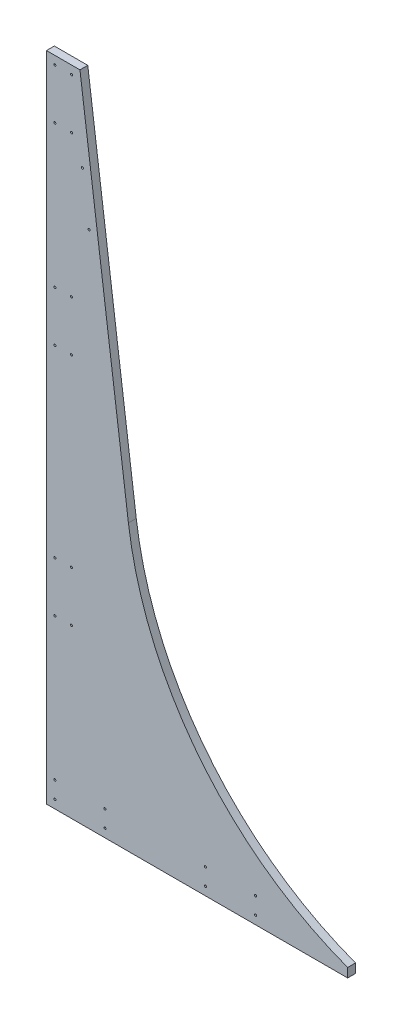
SolidWorks part; units mm, degrees
material "Pine"
ref_plane "Front Plane" through (0, 0, 0) normal (0, 0, 1) x (1, 0, 0)
ref_plane "Top Plane" through (0, 0, 0) normal (0, 1, 0) x (1, 0, 0)
ref_plane "Right Plane" through (0, 0, 0) normal (1, 0, 0) x (0, 0, -1)
sketch "Sketch1" plane through (0, 0, 0) normal (0, 0, 1) x (1, 0, 0)
  line L0 (0, 0) -> (500, 0)
  line L1 (0, 0) -> (0, 990.6)
  line L3 (0, 990.6) -> (50.8, 990.6)
  line L4 (50.8, 990.6) -> (124.3674, 431.8)
  line L7 (457.201, 13.862) -> (457.201, 0)
  arc A9 (124.3674, 431.8) -> (500, 0) centre (638.1166, 499.4364) ccw
  dimension "D18" = 50.8
  dimension "D1" = 500
  dimension "D2" = 990.6
  dimension "D3" = 42.799
  dimension "D4" = 50.8
  dimension "D5" = 558.8
  dimension "D6" = 97.5
extrude "Boss-Extrude1" add sketch "Sketch1" along normal blind 11.9062
sketch "Sketch2" plane through (0, 0, 11.9062) normal (0, 0, 1) x (1, 0, 0)
  line L0 (0, 990.6) -> (50.8, 990.6) construction
  line L1 (0, 0) -> (0, 990.6) construction
  line L2 (12.7, 977.9) -> (38.1, 977.9) construction
  line L3 (38.1, 977.9) -> (38.1, 901.7) construction
  line L4 (38.1, 901.7) -> (12.7, 901.7) construction
  line L5 (12.7, 901.7) -> (12.7, 977.9) construction
  line L6 (12.7, 901.7) -> (12.7, 685.8) construction
  line L7 (12.7, 609.6) -> (38.1, 609.6) construction
  line L8 (12.7, 685.8) -> (12.7, 609.6) construction
  line L9 (38.1, 685.8) -> (12.7, 685.8) construction
  line L10 (12.7, 254) -> (12.7, 38.1) construction
  line L11 (12.7, 254) -> (12.7, 330.2) construction
  line L12 (12.7, 330.2) -> (38.1, 330.2) construction
  line L13 (38.1, 330.2) -> (38.1, 254) construction
  line L14 (38.1, 254) -> (12.7, 254) construction
  line L15 (12.7, 38.1) -> (88.9, 38.1) construction
  line L16 (88.9, 38.1) -> (88.9, 12.7) construction
  line L17 (88.9, 12.7) -> (12.7, 12.7) construction
  line L18 (12.7, 12.7) -> (12.7, 38.1) construction
  line L20 (88.9, 38.1) -> (241.3, 38.1) construction
  line L21 (241.3, 38.1) -> (317.5, 38.1) construction
  line L22 (317.5, 38.1) -> (317.5, 12.7) construction
  line L23 (317.5, 12.7) -> (241.3, 12.7) construction
  line L24 (241.3, 12.7) -> (241.3, 38.1) construction
  circle A0 centre (12.7, 977.9) radius 1.5875
  circle A1 centre (38.1, 977.9) radius 1.5875
  circle A2 centre (12.7, 901.7) radius 1.5875
  circle A3 centre (38.1, 901.7) radius 1.5875
  circle A4 centre (12.7, 609.6) radius 1.5875
  circle A5 centre (38.1, 609.6) radius 1.5875
  circle A6 centre (12.7, 685.8) radius 1.5875
  circle A7 centre (38.1, 685.8) radius 1.5875
  circle A8 centre (12.7, 254) radius 1.5875
  circle A9 centre (38.1, 254) radius 1.5875
  circle A10 centre (12.7, 330.2) radius 1.5875
  circle A11 centre (38.1, 330.2) radius 1.5875
  circle A12 centre (12.7, 38.1) radius 1.5875
  circle A13 centre (12.7, 12.7) radius 1.5875
  circle A14 centre (88.9, 38.1) radius 1.5875
  circle A15 centre (88.9, 12.7) radius 1.5875
  circle A16 centre (241.3, 38.1) radius 1.5875
  circle A17 centre (317.5, 38.1) radius 1.5875
  circle A18 centre (241.3, 12.7) radius 1.5875
  circle A19 centre (317.5, 12.7) radius 1.5875
  dimension "D1" = 3.175
  dimension "D3" = 25.4
  dimension "D4" = 12.7
  dimension "D10" = 279.4
  dimension "D13" = 215.9
  dimension "D2" = 12.7
  dimension "D5" = 76.2
  dimension "D6" = 215.9
  dimension "D7" = 76.2
  dimension "D8" = 25.4
  dimension "D9" = 25.4
  dimension "D11" = 76.2
  dimension "D12" = 25.4
  dimension "D14" = 25.4
  dimension "D15" = 76.2
  dimension "D16" = 25.4
  dimension "D17" = 76.2
  dimension "D18" = 152.4
extrude "Cut-Extrude1" cut sketch "Sketch2" against normal through all
sketch "Sketch3" plane through (0, 0, 11.9062) normal (0, 0, 1) x (1, 0, 0)
  line L0 (64.7422, 787.4) -> (54.7103, 863.6) construction
  line L1 (50.8, 990.6) -> (124.3674, 431.8) construction
  line L3 (0, 990.6) -> (50.8, 990.6) construction
  circle A0 centre (64.7422, 787.4) radius 1.5875
  circle A1 centre (54.7103, 863.6) radius 1.5875
  dimension "D1" = 3.175
  dimension "D2" = 12.7
  dimension "D3" = 127
  dimension "D4" = 76.2
extrude "Cut-Extrude2" cut sketch "Sketch3" against normal through all
